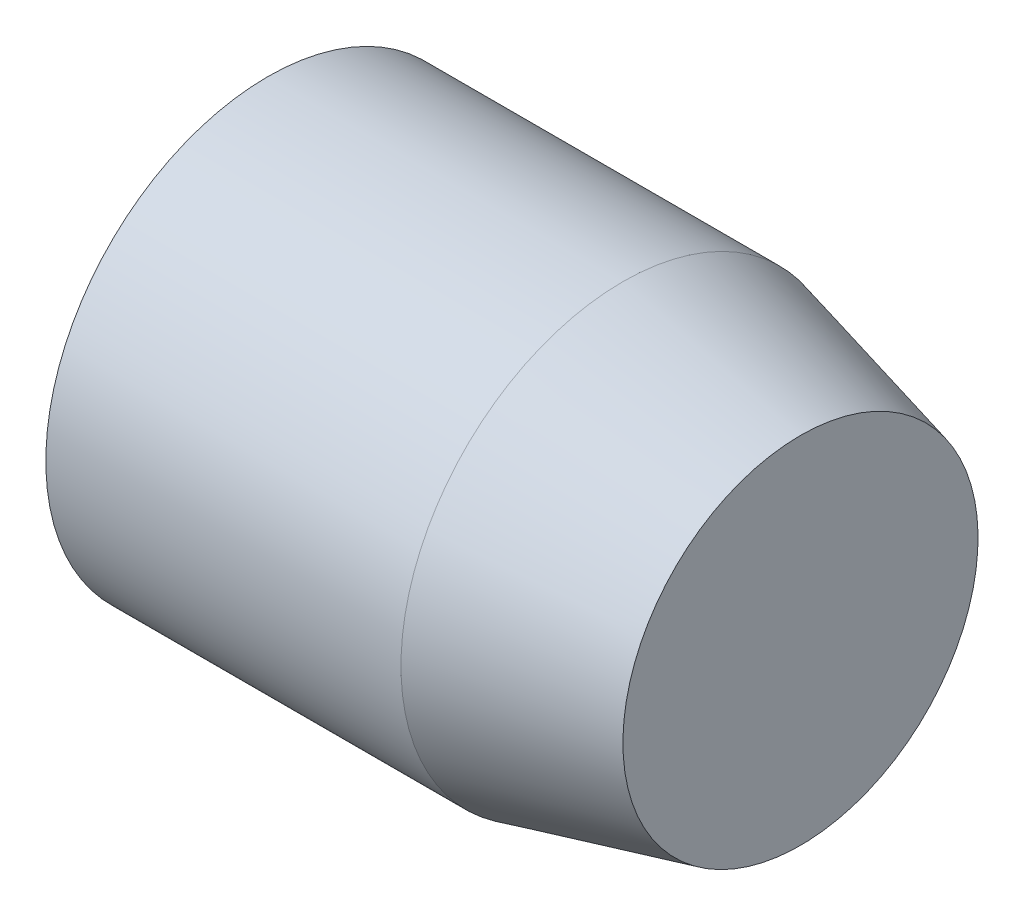
SolidWorks part; units mm, degrees
material "Plain Carbon Steel"
ref_plane "Front Plane" through (0, 0, 0) normal (0, 0, 1) x (1, 0, 0)
ref_plane "Top Plane" through (0, 0, 0) normal (0, 1, 0) x (1, 0, 0)
ref_plane "Right Plane" through (0, 0, 0) normal (1, 0, 0) x (0, 0, -1)
sketch "Sketch1" plane through (0, 0, 0) normal (0, 0, 1) x (1, 0, 0)
  line L0 (0, 0) -> (0, 5)
  line L1 (0, 5) -> (8, 5)
  line L2 (8, 5) -> (12, 4)
  line L3 (12, 4) -> (12, 0)
  line L4 (12, 0) -> (0, 0)
  dimension "D1" = 8
  dimension "D2" = 4
  dimension "D3" = 5
  dimension "D4" = 4
revolve "Revolve1" add sketch "Sketch1" angle 360 about L4
